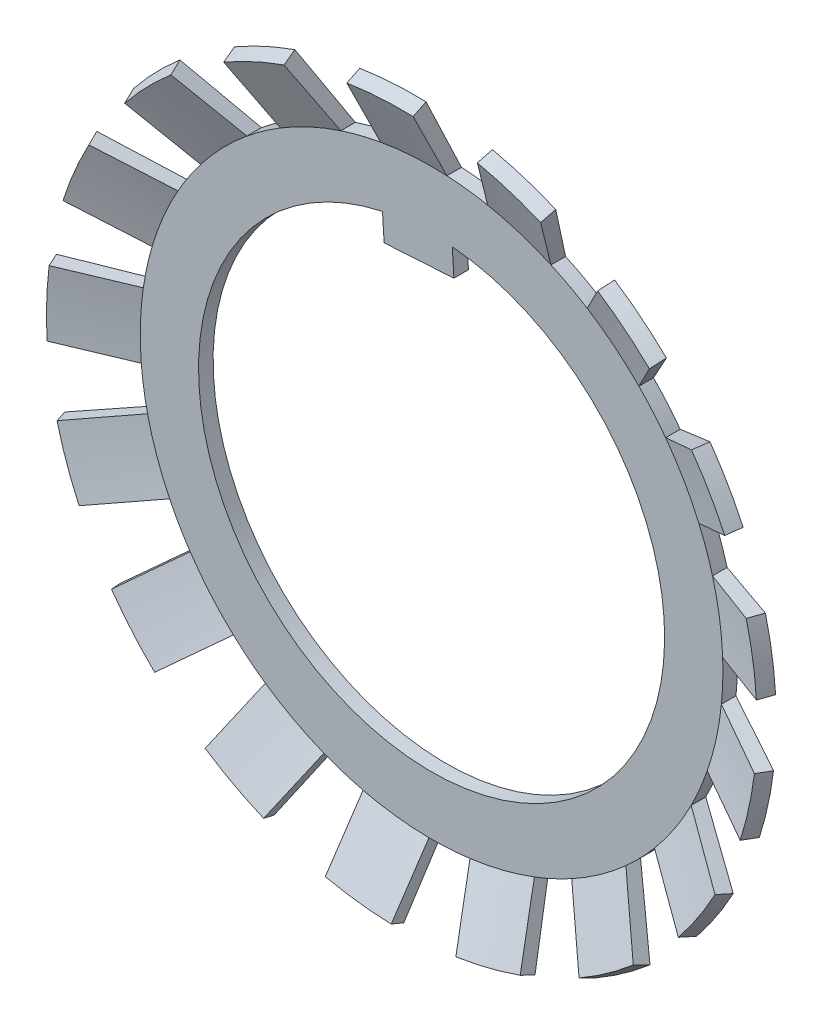
SolidWorks part; units mm, degrees
ref_plane "Front" through (0, 0, 0) normal (0, 0, 1) x (1, 0, 0)
ref_plane "Top" through (0, 0, 0) normal (0, 1, 0) x (1, 0, 0)
ref_plane "Right" through (0, 0, 0) normal (1, 0, 0) x (0, 0, -1)
sketch "Sketch1" plane through (0, 0, 0) normal (1, 0, 0) x (0, 1, 0)
  line L0 (0, -3.811) -> (-25, -3.811)
  line L1 (-25, -3.811) -> (-31, -1.1421)
  line L2 (0, 5.8236) -> (0, -8.1378) construction
  line L4 (-30.492, 0) -> (-25, -2.561)
  line L5 (-25, -2.561) -> (0, -2.561)
  line L6 (0, -2.561) -> (0, -3.811)
  line L7 (-31, -1.1421) -> (-30.492, 0)
  dimension "D1" = 50
  dimension "S1" = 1.25
  dimension "Angle" = 65
  dimension "D" = 62
  dimension "S" = 1.25
revolve "Base-Extrude" add sketch "Sketch1" angle 360 about L2
sketch "Sketch2" plane through (-2.4044, 1.0036, -3.811) normal (0, 0, -1) x (-1, 0, 0)
  line L5 (-22.4888, 13.8831) -> (-27.7124, 16.899)
  line L6 (-25.3388, 8.9468) -> (-30.5624, 11.9626)
  line L9 (-2.4044, 13.9688) -> (-2.4044, -17.023) construction
  line L10 (-2.4044, -1.0036) -> (1.5148, -15.6299) construction
  circle A0 centre (-2.4044, -1.0036) radius 20
  arc A2 (-25.3388, 8.9468) -> (-22.4888, 13.8831) centre (-2.4044, -1.0036) ccw
  arc A4 (-27.7124, 16.899) -> (-30.5624, 11.9626) centre (-2.4044, -1.0036) ccw
  dimension "D1" = 40
  dimension "D9" = 15
extrude "Cut-Extrude" cut sketch "Sketch2" against normal through all flip side to cut
pattern_circular "阵列(圆周)4" count 17 over 360 about axis through (0, 0, 0) along (0, 0, 1) of bodies 109
sketch "草图2" plane through (0, 0, -2.561) normal (0, 0, 1) x (1, 0, 0)
  line L0 (0, 0) -> (-1.9084, 30.9412) construction
  line L1 (1.917, 17.6515) -> (1.777, 19.9209)
  line L2 (-4.0716, 17.2821) -> (-4.2116, 19.5515)
  line L3 (-4.0716, 17.2821) -> (1.917, 17.6515)
  line L5 (2.9943, 0.1847) -> (1.0859, 31.1259) construction
  line L6 (-2.9943, -0.1847) -> (-4.9027, 30.7565) construction
  circle A0 centre (0, 0) radius 20 construction
  arc A1 (1.777, 19.9209) -> (-4.2116, 19.5515) centre (0, 0) ccw
  arc A2 (0.9443, 30.9856) -> (-4.7449, 30.6347) centre (0, 0) ccw construction
  dimension "D1" = 3
  dimension "D2" = 3
extrude "凸台-拉伸1" add sketch "草图2" against normal up to surface (1.25 mm away) up to face at (17.0043, 10.5286, -3.811)
equation "\"S1@Sketch1\" = \"S@Sketch1\""
equation "\"D1@Extrude1\"=\"S@Sketch1\""
